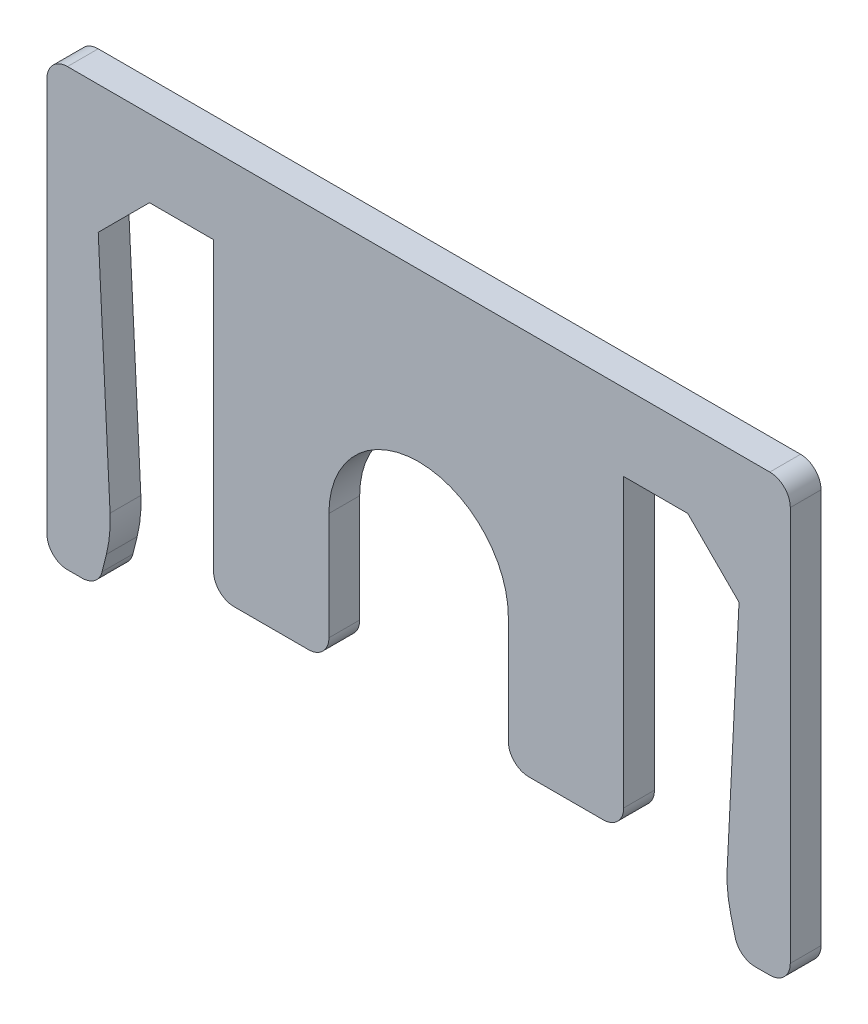
SolidWorks part; units mm, degrees
ref_plane "Front Plane" through (0, 0, 0) normal (0, 0, 1) x (1, 0, 0)
ref_plane "Top Plane" through (0, 0, 0) normal (0, 1, 0) x (1, 0, 0)
ref_plane "Right Plane" through (0, 0, 0) normal (1, 0, 0) x (0, 0, -1)
sketch "Sketch1" plane through (0, 0, 0) normal (0, 0, 1) x (1, 0, 0)
  line L0 (-12.5, 0) -> (-10.5, 0) construction
  line L1 (-10.5, 0) -> (-12.5, -2)
  line L2 (-12.5, -2) -> (-12.5, 0) construction
  line L3 (12.5, 0) -> (12.5, -2) construction
  line L4 (12.5, -2) -> (10.5, 0)
  line L5 (10.5, 0) -> (12.5, 0) construction
  line L6 (-12.5, -2) -> (-12, -12)
  line L7 (-12, -12) -> (-12.5, -14)
  line L8 (-12.5, -14) -> (-12.5, -2) construction
  line L9 (12.5, -2) -> (12.5, -14) construction
  line L10 (12.5, -14) -> (12, -12)
  line L11 (12, -12) -> (12.5, -2)
  line L12 (-10.5, 0) -> (-8, 0) construction
  line L13 (-3.5, -12) -> (3.5, -12) construction
  line L14 (-12.5, -14) -> (-14.5, -14)
  line L15 (-12.5, -14) -> (-12.5, -2) construction
  line L16 (-12.5, 3) -> (-14.5, 3)
  line L17 (-14.5, -14) -> (-14.5, 3)
  line L18 (12.5, -14) -> (14.5, -14)
  line L19 (12.5, -14) -> (12.5, -2) construction
  line L20 (12.5, 3) -> (14.5, 3)
  line L21 (14.5, -14) -> (14.5, 3)
  line L22 (-12.5, 3) -> (12.5, 3)
  line L23 (-12.5, 3) -> (-12.5, 0) construction
  line L24 (-10.5, 0) -> (-8, 0)
  line L25 (12.5, 3) -> (12.5, 0) construction
  line L26 (-3.5, -7) -> (3.5, -7) construction
  line L27 (-3.5, -7) -> (-3.5, -12)
  line L28 (-3.5, -12) -> (3.5, -12) construction
  line L29 (3.5, -7) -> (3.5, -12)
  line L30 (-8, -12) -> (-3.5, -12)
  line L31 (-8, -12) -> (-8, 0)
  line L32 (-8, 0) -> (8, 0) construction
  line L33 (8, -12) -> (8, 0)
  line L34 (-4.5, -3) -> (4.5, -3) construction
  line L35 (-4.5, -3) -> (-4.5, -12) construction
  line L36 (-4.5, -12) -> (-3.5, -12) construction
  line L37 (4.5, -3) -> (4.5, -12) construction
  line L38 (-4.5, -3) -> (4.5, -12) construction
  line L39 (-4.5, -12) -> (4.5, -3) construction
  line L40 (3.5, -12) -> (8, -12)
  line L41 (-3.5, -12) -> (3.5, -12) construction
  line L42 (3.5, -12) -> (4.5, -12) construction
  line L43 (-8, 0) -> (8, 0) construction
  line L44 (8, 0) -> (10.5, 0) construction
  line L45 (-8, 0) -> (8, 0) construction
  line L46 (8, 0) -> (10.5, 0)
  line L47 (-12.5, -2) -> (-12.5, 0) construction
  line L48 (-12.5, 0) -> (-12.5, 3) construction
  line L49 (-12.5, 0) -> (-10.5, 0) construction
  line L50 (12.5, 0) -> (12.5, 3) construction
  line L51 (10.5, 0) -> (12.5, 0) construction
  line L52 (12.5, -2) -> (12.5, 0) construction
  arc A0 (3.5, -7) -> (-3.5, -7) centre (0, -7) ccw
  arc A1 (-3.5, -7) -> (-2.2122, -9.7122) centre (0, -7) ccw construction
  arc A2 (-2.2122, -9.7122) -> (2.2122, -9.7122) centre (0, -7) ccw construction
  arc A3 (2.2122, -9.7122) -> (3.5, -7) centre (0, -7) ccw construction
  point P28 (0, 0)
  point P29 (0, -7.5)
  point P34 (5.8042, -3.4177)
  point P35 (-0.1925, -6.6497)
  point P37 (0, -6.898)
  point P38 (0, -7.5)
  point P39 (0, 0)
  point P40 (0, -7.5)
  point P41 (0, -5.5852)
  dimension "D12" = 7
  dimension "D1" = 2
  dimension "D2" = 2
  dimension "D3" = 2
  dimension "D4" = 0.5
  dimension "D5" = 2
  dimension "D6" = 10
  dimension "D7" = 0.5
  dimension "D8" = 21
  dimension "D9" = 2
  dimension "D10" = 2
  dimension "D11" = 3
  dimension "D13" = 16
  dimension "D14" = 9
  dimension "D15" = 9
  dimension "D16" = 10.5
  dimension "D17" = 0.5
extrude "Boss-Extrude1" add sketch "Sketch1" along normal blind 1.2
fillet "Fillet1" radius 5 2 edges at (-12, -12, 0.6) (12, -12, 0.6)
fillet "Fillet2" radius 0.8 10 edges at (14.5, 3, 0.6) (-14.5, 3, 0.6) (14.5, -14, 0.6) (-14.5, -14, 0.6) (12.5, -14, 0.6) (-12.5, -14, 0.6) (-8, -12, 0.6) (8, -12, 0.6) (3.5, -12, 0.6) (-3.5, -12, 0.6)
